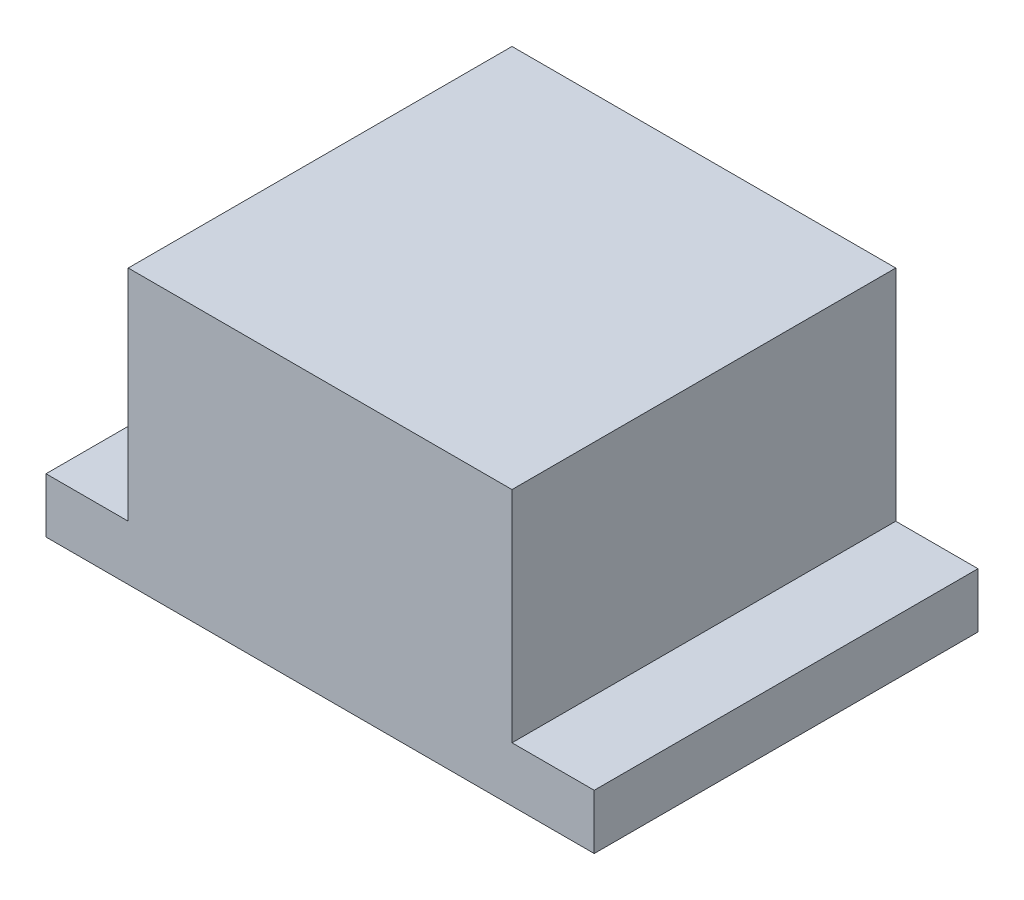
SolidWorks part; units mm, degrees
ref_plane "Front" through (0, 0, 0) normal (0, 0, 1) x (1, 0, 0)
ref_plane "Top" through (0, 0, 0) normal (0, 1, 0) x (1, 0, 0)
ref_plane "Right" through (0, 0, 0) normal (1, 0, 0) x (0, 0, -1)
sketch "Эскиз1" plane through (0, 0, 0) normal (0, 0, 1) x (1, 0, 0)
  line L0 (-2.5, 0) -> (2.5, 0)
  line L1 (2.5, 0) -> (2.5, 0.5)
  line L2 (2.5, 0.5) -> (1.75, 0.5)
  line L3 (1.75, 0.5) -> (1.75, 2.5)
  line L4 (1.75, 2.5) -> (-1.75, 2.5)
  line L5 (-1.75, 2.5) -> (-1.75, 0.5)
  line L6 (-1.75, 0.5) -> (-2.5, 0.5)
  line L7 (-2.5, 0.5) -> (-2.5, 0)
  point P3 (0, 2.5)
  dimension "D1" = 5
  dimension "D2" = 3.5
  dimension "D3" = 0.5
  dimension "D4" = 2.5
extrude "Бобышка-Вытянуть1" add sketch "Эскиз1" along normal blind 3.5
